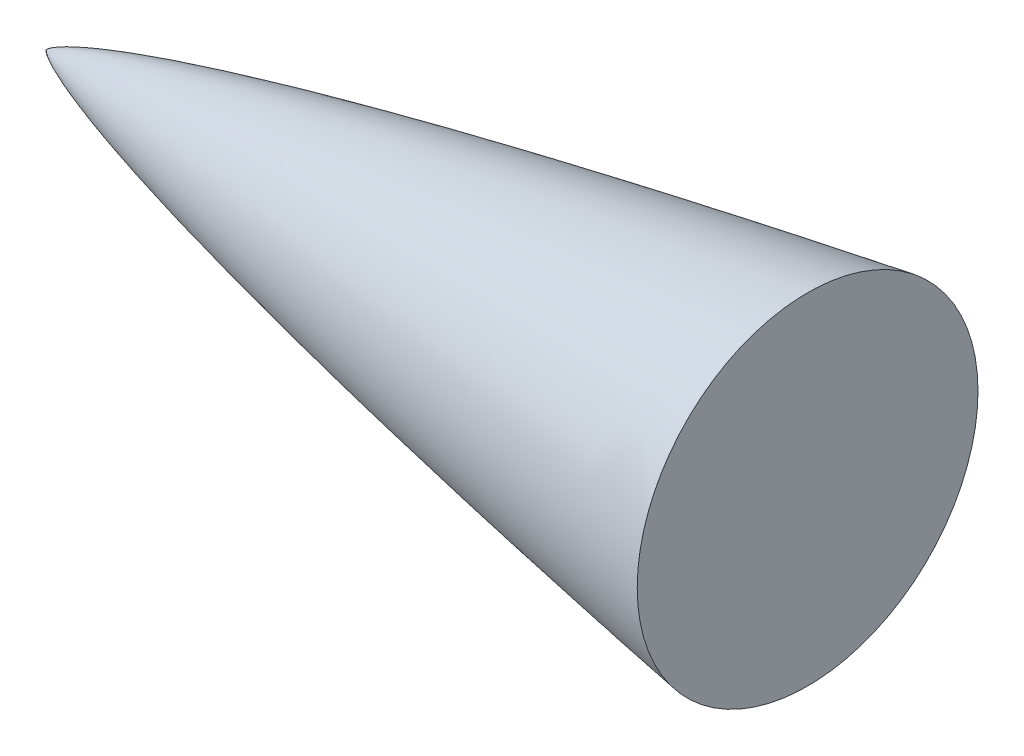
SolidWorks part; units mm, degrees
ref_plane "Front Plane" through (0, 0, 0) normal (0, 0, 1) x (1, 0, 0)
ref_plane "Top Plane" through (0, 0, 0) normal (0, 1, 0) x (1, 0, 0)
ref_plane "Right Plane" through (0, 0, 0) normal (1, 0, 0) x (0, 0, -1)
sketch "Sketch1" plane through (0, 0, 0) normal (0, 1, 0) x (1, 0, 0)
  line L0 (0, 0) -> (635, 0)
  line L1 (635, 0) -> (635, 65.405)
  spline S0 degree 4 poles (0, 0) (0.0022, 0.0063) (0.0075, 0.0184) (0.0223, 0.0404) (0.057, 0.0804) (0.1098, 0.1304) (0.1816, 0.1889) (0.2836, 0.2634) (0.4063, 0.3444) (0.5502, 0.4318) (0.7155, 0.5251) (0.9567, 0.6537) (1.3318, 0.8391) (1.9703, 1.1275) (3.1158, 1.5922) (5.1634, 2.3284) (8.9332, 3.5155) (16.022, 5.4463) (28.2617, 8.305) (49.1788, 12.5136) (77.9573, 17.4873) (112.8708, 22.8061) (151.8575, 28.1242) (190.9036, 32.9827) (229.9952, 37.4592) (269.1232, 41.6038) (308.2821, 45.4454) (347.4678, 49.0026) (386.6776, 52.2836) (425.9094, 55.2895) (465.1619, 58.0128) (504.4341, 60.4362) (538.8141, 62.2665) (568.2945, 63.5925) (591.9899, 64.4666) (607.8766, 64.942) (620.8678, 65.2384) (628.9431, 65.3608) (632.981, 65.3999) (635, 65.405) knots 0 0 0 0 0 0.000041 0.000083 0.000165 0.000331 0.000496 0.000661 0.000955 0.001249 0.001549 0.001849 0.002664 0.003866 0.00593 0.009578 0.01627 0.028579 0.051871 0.088176 0.149698 0.211221 0.272743 0.334265 0.395788 0.45731 0.518832 0.580355 0.641877 0.703399 0.764922 0.826444 0.887966 0.918727 0.949489 0.974744 0.987372 1 1 1 1 1 construction
  spline S1 degree 4 poles (0, 0) (0.0022, 0.0063) (0.0075, 0.0184) (0.0223, 0.0404) (0.057, 0.0804) (0.1098, 0.1304) (0.1816, 0.1889) (0.2836, 0.2634) (0.4063, 0.3444) (0.5502, 0.4318) (0.7155, 0.5251) (0.9567, 0.6537) (1.3318, 0.8391) (1.9703, 1.1275) (3.1158, 1.5922) (5.1634, 2.3284) (8.9332, 3.5155) (16.022, 5.4463) (28.2617, 8.305) (49.1788, 12.5136) (77.9573, 17.4873) (112.8708, 22.8061) (151.8575, 28.1242) (190.9036, 32.9827) (229.9952, 37.4592) (269.1232, 41.6038) (308.2821, 45.4454) (347.4678, 49.0026) (386.6776, 52.2836) (425.9094, 55.2895) (465.1619, 58.0128) (504.4341, 60.4362) (538.8141, 62.2665) (568.2945, 63.5925) (591.9899, 64.4666) (607.8766, 64.942) (620.8678, 65.2384) (628.9431, 65.3608) (632.981, 65.3999) (635, 65.405) knots 0 0 0 0 0 0.000041 0.000083 0.000165 0.000331 0.000496 0.000661 0.000955 0.001249 0.001549 0.001849 0.002664 0.003866 0.00593 0.009578 0.01627 0.028579 0.051871 0.088176 0.149698 0.211221 0.272743 0.334265 0.395788 0.45731 0.518832 0.580355 0.641877 0.703399 0.764922 0.826444 0.887966 0.918727 0.949489 0.974744 0.987372 1 1 1 1 1
  dimension "D1" = 65.405
revolve "Revolve1" add sketch "Sketch1" angle 360 about L0
ref_plane "Plane1" through (0, 0, -203.2) normal (0, 0, 1) x (1, 0, 0)
sketch "Sketch2" plane through (0, 0, -203.2) normal (0, 0, 1) x (1, 0, 0)
  line L1 (711.2, 88.9) -> (76.2, 88.9)
  line L2 (711.2, 88.9) -> (711.2, -88.9)
  line L3 (711.2, -88.9) -> (76.2, -88.9)
  line L4 (76.2, 88.9) -> (76.2, -88.9)
  point P4 (76.2, 0)
  dimension "D1" = 76.2
  dimension "D2" = 177.8
  dimension "D3" = 635
extrude "Cut-Extrude1" cut sketch "Sketch2" along normal blind 337.058
